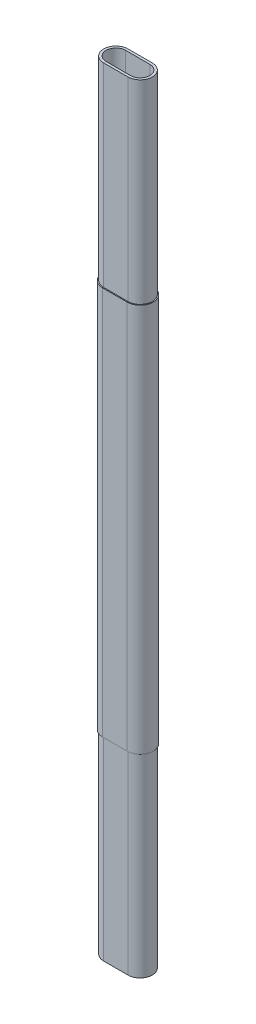
SolidWorks part; units mm, degrees
material "Cast Alloy Steel"
ref_plane "Front Plane" through (0, 0, 0) normal (0, 0, 1) x (1, 0, 0)
ref_plane "Top Plane" through (0, 0, 0) normal (0, 1, 0) x (1, 0, 0)
ref_plane "Right Plane" through (0, 0, 0) normal (1, 0, 0) x (0, 0, -1)
ref_plane "Plane1" through (0, 0, 0) normal (0, 1, 0) x (1, 0, 0)
sketch "Sketch1" plane through (0, 0, 0) normal (0, 1, 0) x (1, 0, 0)
  line L0 (-0.25, 0.25) -> (0.25, 0.25)
  line L1 (0.25, -0.25) -> (-0.25, -0.25)
  arc A0 (-0.25, 0.25) -> (-0.25, -0.25) centre (-0.25, 0) ccw
  arc A1 (0.25, -0.25) -> (0.25, 0.25) centre (0.25, 0) ccw
extrude "Extrude-Thin2" add sketch "Sketch1" along normal blind 8 and the other way blind 8 thin
ref_plane "Plane2" through (0, 0, 0) normal (0, 1, 0) x (-1, 0, 0)
sketch "Sketch2" plane through (0, 0, 0) normal (0, 1, 0) x (-1, 0, 0)
  line L0 (0.25, 0.25) -> (-0.25, 0.25)
  line L1 (0.25, -0.25) -> (-0.25, -0.25)
  arc A0 (0.25, -0.25) -> (0.25, 0.25) centre (0.25, 0) ccw
  arc A1 (-0.25, 0.25) -> (-0.25, -0.25) centre (-0.25, 0) ccw
extrude "Extrude-Thin4" add sketch "Sketch2" along normal blind 4 and the other way blind 4 thin
